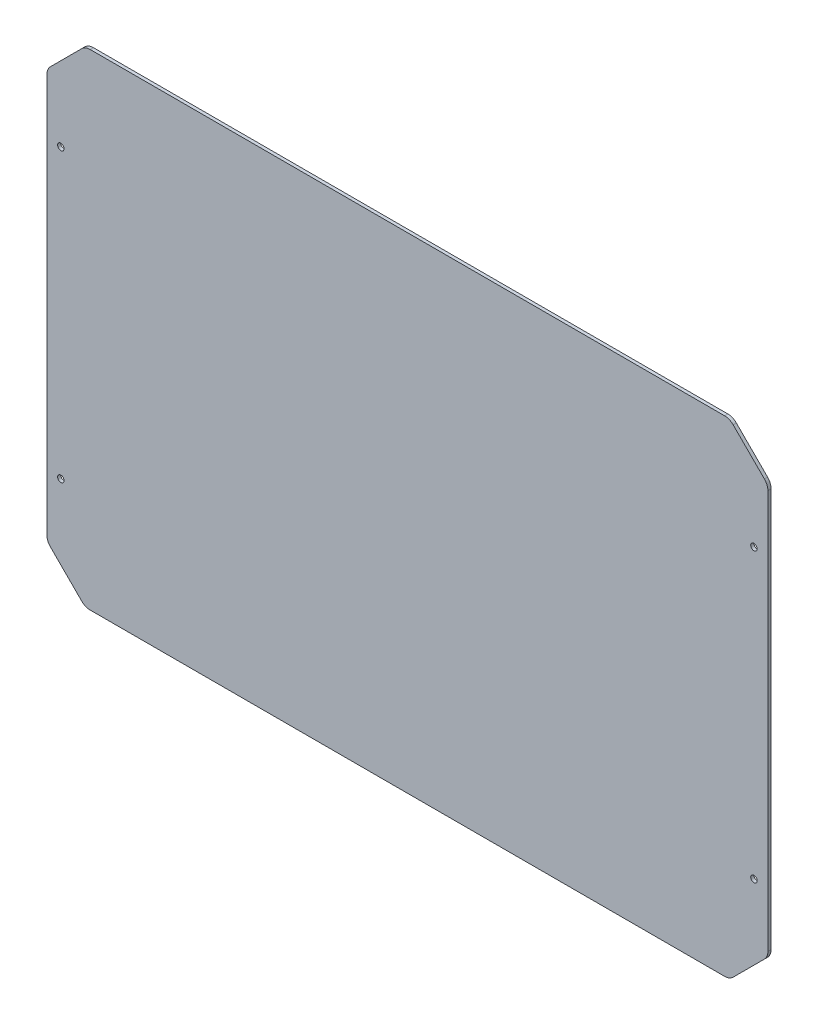
SolidWorks part; units mm, degrees
material "Glass"
ref_plane "Plan de face" through (0, 0, 0) normal (0, 0, 1) x (1, 0, 0)
ref_plane "Plan de dessus" through (0, 0, 0) normal (0, 1, 0) x (1, 0, 0)
ref_plane "Plan de droite" through (0, 0, 0) normal (1, 0, 0) x (0, 0, -1)
sketch "Sketch2" plane through (0, 0, 0) normal (0, 0, 1) x (1, 0, 0)
  line L24 (-451.5, 256) -> (-451.5, -256)
  line L25 (-403.5, -304) -> (403.5, -304)
  line L26 (451.5, 256) -> (451.5, -256)
  line L27 (-403.5, 304) -> (403.5, 304)
  line L28 (-451.5, -256) -> (-403.5, -304)
  line L29 (403.5, -304) -> (451.5, -256)
  line L30 (-403.5, 304) -> (-451.5, 256)
  line L31 (403.5, 304) -> (451.5, 256)
  line L40 (0, 304) -> (0, -304) construction
  line L44 (-434, -180) -> (434, -180) construction
  line L45 (-434, -180) -> (-434, 180) construction
  line L46 (-434, 180) -> (434, 180) construction
  line L47 (434, -180) -> (434, 180) construction
  line L48 (-434, -180) -> (434, 180) construction
  line L49 (-434, 180) -> (434, -180) construction
  circle A1 centre (-434, 180) radius 4.05
  circle A2 centre (-434, -180) radius 4.05
  circle A3 centre (434, -180) radius 4.05
  circle A4 centre (434, 180) radius 4.05
  point P0 (-432.1569, 180)
  point P50 (0, 0)
  dimension "D28" = 8.1
  dimension "D3" = 451.5
  dimension "D4" = 17.5
  dimension "D17" = 608
  dimension "D18" = 903
  dimension "D23" = 360
extrude "Boss-Extrude1" add sketch "Sketch2" along normal blind 4
fillet "Fillet1" radius 15 8 edges at (-451.5, -256, 2) (-403.5, -304, 2) (403.5, -304, 2) (451.5, -256, 2) (451.5, 256, 2) (403.5, 304, 2) (-403.5, 304, 2) (-451.5, 256, 2)
